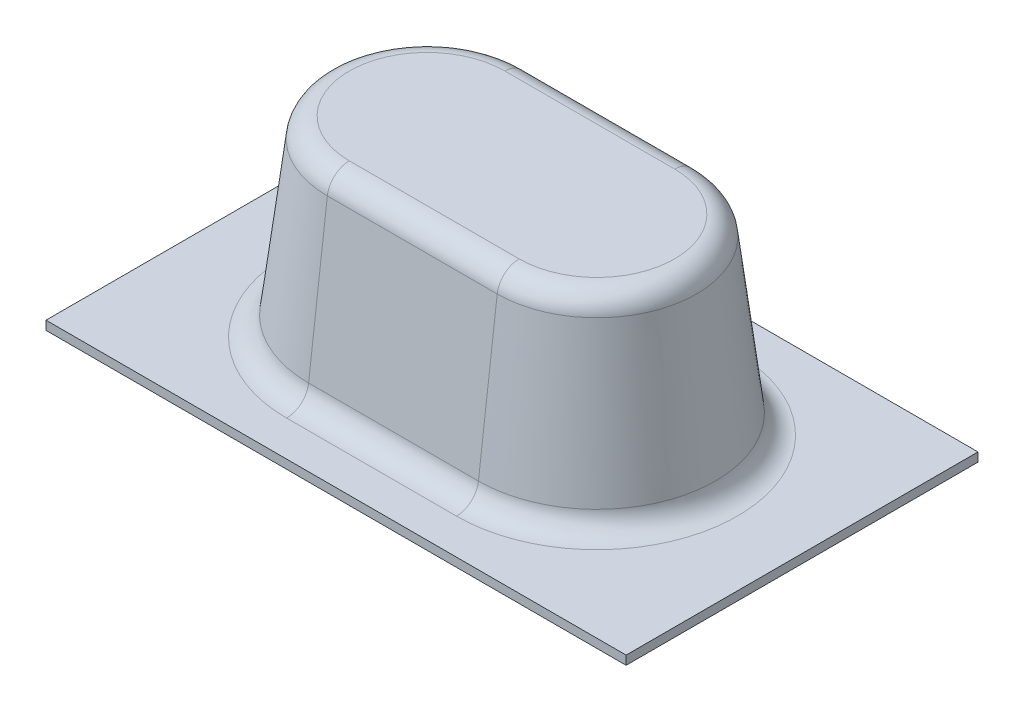
SolidWorks part; units mm, degrees
ref_plane "Front Plane" through (0, 0, 0) normal (0, 0, 1) x (1, 0, 0)
ref_plane "Top Plane" through (0, 0, 0) normal (0, 1, 0) x (1, 0, 0)
ref_plane "Right Plane" through (0, 0, 0) normal (1, 0, 0) x (0, 0, -1)
sketch "Sketch1" plane through (0, 0, 0) normal (0, 1, 0) x (1, 0, 0)
  line L1 (16.65, 10.1) -> (-16.65, 10.1)
  line L2 (16.65, 10.1) -> (16.65, -10.1)
  line L3 (16.65, -10.1) -> (-16.65, -10.1)
  line L4 (-16.65, 10.1) -> (-16.65, -10.1)
  line L5 (16.65, 10.1) -> (-16.65, -10.1) construction
  line L6 (16.65, -10.1) -> (-16.65, 10.1) construction
  point P0 (0, 0)
  dimension "D1" = 20.2
  dimension "D2" = 33.3
extrude "Boss-Extrude1" add sketch "Sketch1" along normal blind 0.508
sketch "Sketch2" plane through (0, 0, 0) normal (0, 1, 0) x (1, 0, 0)
  line L1 (-4.875, 7) -> (4.875, 7)
  line L2 (-4.875, 7) -> (-4.875, -7) construction
  line L3 (-4.875, -7) -> (4.875, -7)
  line L4 (4.875, 7) -> (4.875, -7) construction
  line L5 (-4.875, 7) -> (4.875, -7) construction
  line L6 (-4.875, -7) -> (4.875, 7) construction
  arc A1 (4.875, -7) -> (4.875, 7) centre (4.875, 0) ccw
  arc A2 (-4.875, -7) -> (-4.875, 7) centre (-4.875, 0) cw
  point P0 (0, 0)
  dimension "D1" = 23.75
  dimension "D2" = 14
extrude "Boss-Extrude2" add sketch "Sketch2" along normal blind 11.5 draft 7
fillet "Fillet1" radius 1.27 4 edges at (-10.463, 11.5, 0) (0, 11.5, -5.588) (10.463, 11.5, 0) (0, 11.5, 5.588)
fillet "Fillet4" radius 1.27 4 edges at (-11.8126, 0.508, 0) (0, 0.508, -6.9376) (11.8126, 0.508, 0) (0, 0.508, 6.9376)
